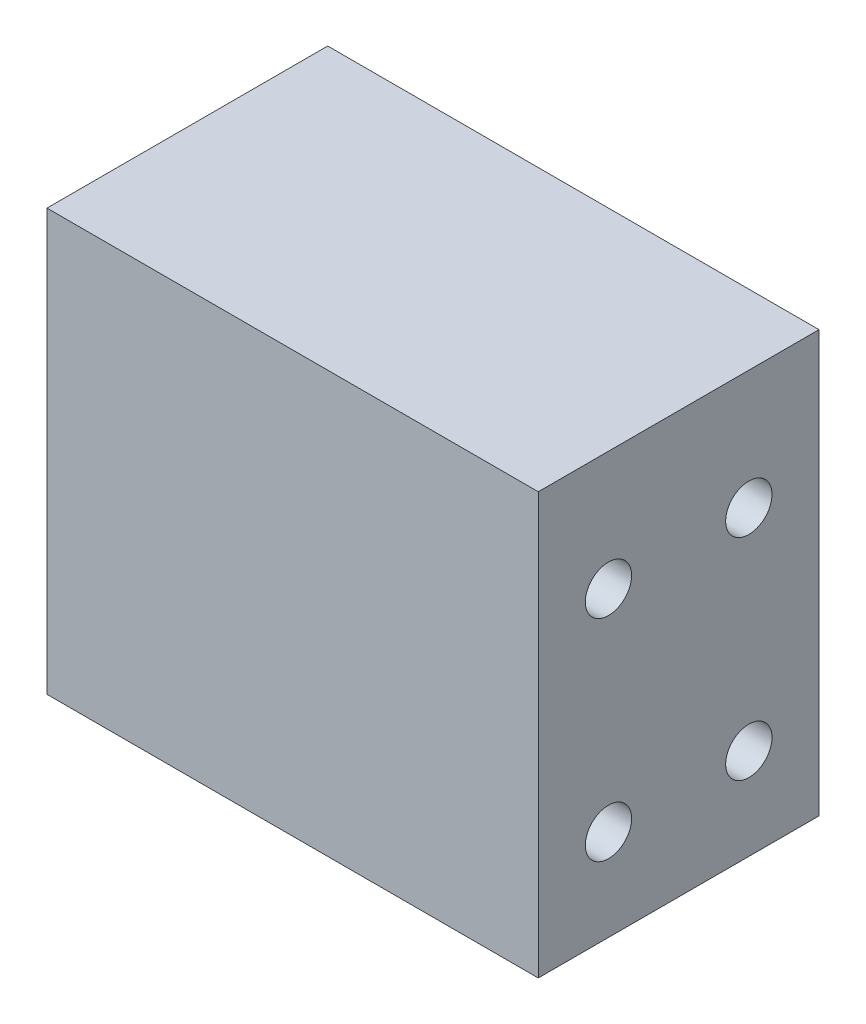
SolidWorks part; units mm, degrees
material "6061-T6 (SS)"
ref_plane "Front Plane" through (0, 0, 0) normal (0, 0, 1) x (1, 0, 0)
ref_plane "Top Plane" through (0, 0, 0) normal (0, 1, 0) x (1, 0, 0)
ref_plane "Right Plane" through (0, 0, 0) normal (1, 0, 0) x (0, 0, -1)
sketch "Sketch1" plane through (0, 0, 0) normal (0, 0, 1) x (1, 0, 0)
  line L1 (0, 0) -> (-35, 0)
  line L2 (0, 0) -> (0, 30)
  line L3 (0, 30) -> (-35, 30)
  line L4 (-35, 0) -> (-35, 30)
  dimension "D1" = 35
  dimension "D2" = 30
extrude "Boss-Extrude1" add sketch "Sketch1" along normal blind 20
ref_plane "Plane1" through (-17.5, 0, 0) normal (-1, 0, 0) x (0, 0, 1)
sketch "Sketch2" plane through (0, 0, 20) normal (0, 0, 1) x (1, 0, 0)
  line L0 (0, 30) -> (-35, 30) construction
  line L1 (-35, 30) -> (-35, 0) construction
  circle A0 centre (-17.5, 15) radius 5
  point P5 (-17.5, 30)
  point P9 (-35, 15)
  dimension "D1" = 10
extrude "Cut-Extrude1" [suppressed] cut sketch "Sketch2" against normal through all
hole_wizard "CBORE for M2 SHCS1" [suppressed] positions "Sketch3" profile "Sketch4" counterbore size "M2" standard "ANSI Metric"
sketch "Sketch3" plane through (0, 0, 0) normal (0, 0, -1) x (-1, 0, 0)
  line L4 (17.5, 22.9875) -> (17.5, 7.9875)
  line L5 (0, 26.975) -> (35, 26.975) construction
  line L7 (35, 26.975) -> (35, 0) construction
  point P2 (17.5, 7.9875)
  point P116 (17.5, 22.9875)
  point P121 (17.5, 26.975)
  point P141 (17.5, 15.4875)
  point P144 (35, 13.4875)
  dimension "D1" = 15
  dimension "D2" = 2
sketch "Sketch4" plane through (-17.5, 7.9875, 0) normal (1, 0, 0) x (0, 1, 0)
  line L0 (0, 0) -> (0, 20)
  line L1 (0, 20) -> (1.2, 20)
  line L3 (1.2, 20) -> (1.2, 2)
  line L4 (1.2, 2) -> (2.2, 2)
  line L5 (2.2, 2) -> (2.2, 0)
  line L7 (2.2, 0) -> (0, 0)
  line L11 (0, -6.35) -> (0, 107.95) construction
  dimension "Thru Hole Dia." = 2.4
  dimension "Thru Hole Depth" = 20
  dimension "C'Bore Dia." = 4.4
  dimension "C'Bore Depth" = 2
hole_wizard "M4x0.7 Tapped Hole1" positions "Sketch5" profile "Sketch6" tap size "M4x0.7" standard "ANSI Metric"
sketch "Sketch5" plane through (-35, 0, 0) normal (-1, 0, 0) x (0, 0, 1)
  line L1 (5, 21.5125) -> (15, 21.5125)
  line L2 (5, 21.5125) -> (5, 6.5125)
  line L3 (5, 6.5125) -> (15, 6.5125)
  line L4 (15, 21.5125) -> (15, 6.5125)
  line L6 (20, 30) -> (20, 0) construction
  point P1 (5, 21.5125)
  point P2 (15, 6.5125)
  point P71 (5, 6.5125)
  point P72 (15, 21.5125)
  point P79 (15, 14.0125)
  point P80 (20, 15)
  dimension "D1" = 10
  dimension "D2" = 15
  dimension "D3" = 0.9875
  dimension "D4" = 5
sketch "Sketch6" plane through (-35, 21.5125, 5) normal (0, 1, 0) x (0, 0, 1)
  line L0 (0, 0) -> (0, 14.4914)
  line L1 (0, 14.4914) -> (1.65, 13.5)
  line L2 (1.65, 13.5) -> (1.65, 0)
  line L5 (1.65, 0) -> (0, 0)
  line L10 (0, 14.4914) -> (-1.65, 13.5) construction
  line L11 (0, -6.35) -> (0, 107.95) construction
  dimension "Tap Drill Dia." = 3.3
  dimension "Tap Drill Depth" = 13.5
  dimension "Drill Angle" = 118
mirror "Mirror1" about plane through (-17.5, 0, 0) normal (-1, 0, 0) of "M4x0.7 Tapped Hole1"
